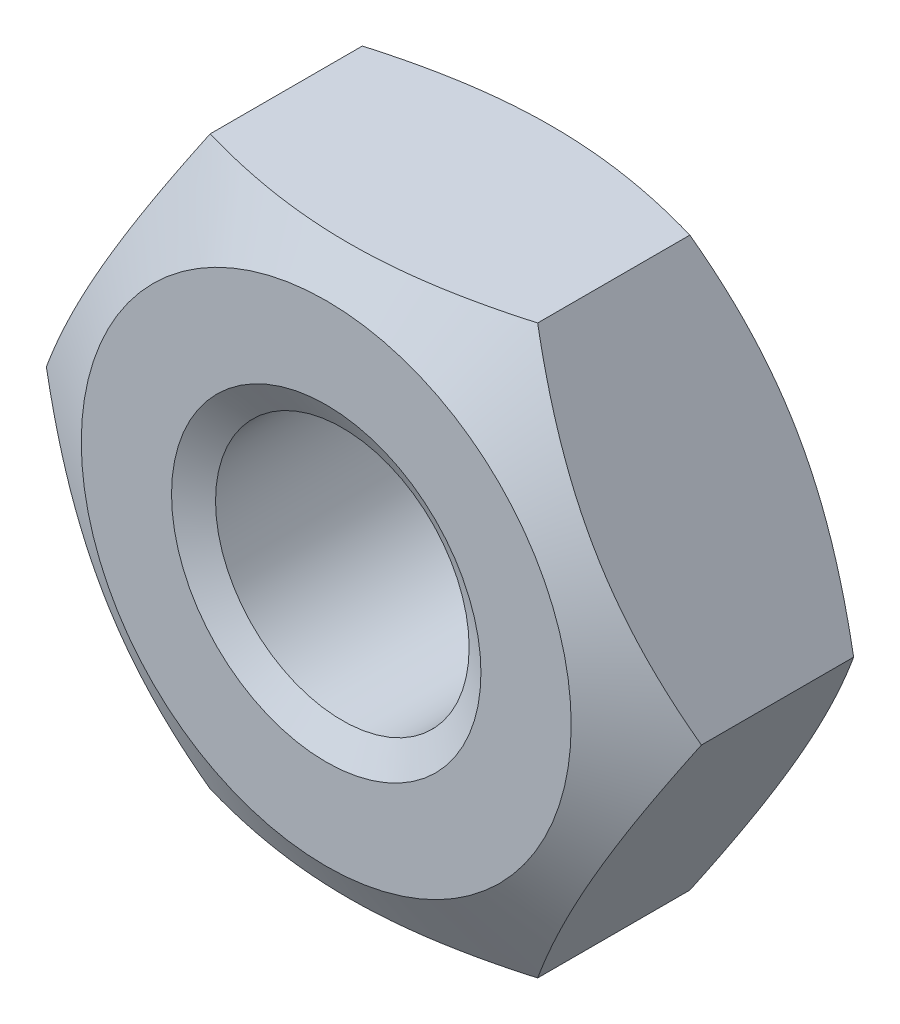
SolidWorks part; units mm, degrees
ref_plane "Front" through (0, 0, 0) normal (0, 0, 1) x (1, 0, 0)
ref_plane "Top" through (0, 0, 0) normal (0, 1, 0) x (1, 0, 0)
ref_plane "Right" through (0, 0, 0) normal (1, 0, 0) x (0, 0, -1)
sketch "Sketch1" plane through (0, 0, 0) normal (0, 0, 1) x (1, 0, 0)
  line L1 (3.1754, 0) -> (1.5877, 2.75)
  line L2 (1.5877, 2.75) -> (-1.5877, 2.75)
  line L3 (-1.5877, 2.75) -> (-3.1754, 0)
  line L4 (-3.1754, 0) -> (-1.5877, -2.75)
  line L5 (-1.5877, -2.75) -> (1.5877, -2.75)
  line L6 (1.5877, -2.75) -> (3.1754, 0)
  circle A0 centre (0, 0) radius 2.75 construction
  circle A1 centre (0, 0) radius 1.2295
  dimension "D" = 2.459
  dimension "s" = 5.5
extrude "BaseNut" add sketch "Sketch1" against normal blind 2.4
cosmetic thread "ThreadCosmetic1" [suppressed] parameters "D"=3
sketch "Sketch2" plane through (0, 0, 0) normal (0, 1, 0) x (1, 0, 0)
  line L0 (-3.1754, 2.4) -> (-2.375, 2.4)
  line L2 (-2.375, 2.4) -> (-3.1754, 1.9379)
  line L3 (-3.1754, 1.9379) -> (-3.1754, 2.4)
  line L4 (0, 3.3759) -> (0, -9.8171) construction
  line L6 (-9.7712, 1.2) -> (9.8853, 1.2) construction
  line L7 (-3.1754, 0.4621) -> (-3.1754, 0)
  line L8 (-2.375, 0) -> (-3.1754, 0.4621)
  line L9 (-3.1754, 0) -> (-2.375, 0)
  dimension "D1" = 30
  dimension "dw" = 4.75
  dimension "D2" = 1.2
revolve "Double-Chamfer" cut sketch "Sketch2" angle 360 about L4
chamfer "EndChamfer" distance 0.2705 angle 30 2 edges at (1.2295, 0, -2.4) (1.2295, 0, 0)
sketch "Sketch3" plane through (0, 0, 0) normal (0, 1, 0) x (1, 0, 0)
  line L0 (-1.4638, 2.1295) -> (-1.2295, 1.9942)
  line L1 (-1.2295, 1.9942) -> (-0.959, 1.9942)
  line L2 (-0.959, 1.9942) -> (-0.959, 2.2647)
  line L3 (-0.959, 2.2647) -> (-1.2295, 2.2647)
  line L4 (-1.2295, 2.2647) -> (-1.4638, 2.1295)
  line L5 (0, 7.4383) -> (0, 16.8806) construction
  dimension "D1" = 0.2705
  dimension "D2" = 2.459
revolve "Cut-Revolve10" [suppressed] cut sketch "Sketch3" angle 360 about L5
pattern_linear "LPattern10" [suppressed] count 7 spacing 0.3246 along (0, 0, -1)
equation "\"dw@Sketch2\" = \"s@Sketch1\"-0.75"
equation "\"D2@Sketch2\" = \"m@BaseNut\" / 2"
equation "\"D2@Sketch3\" = \"D@Sketch1\""
equation "\"D1@Sketch3\" =  (\"D@ThreadCosmetic1\"   - \"D@Sketch1\")  / 2"
equation "\"D3@LPattern10\" = \"D1@Sketch3\" * 1.2"
equation "\"D1@LPattern10\" = \"m@BaseNut\"/\"D3@LPattern10\""
